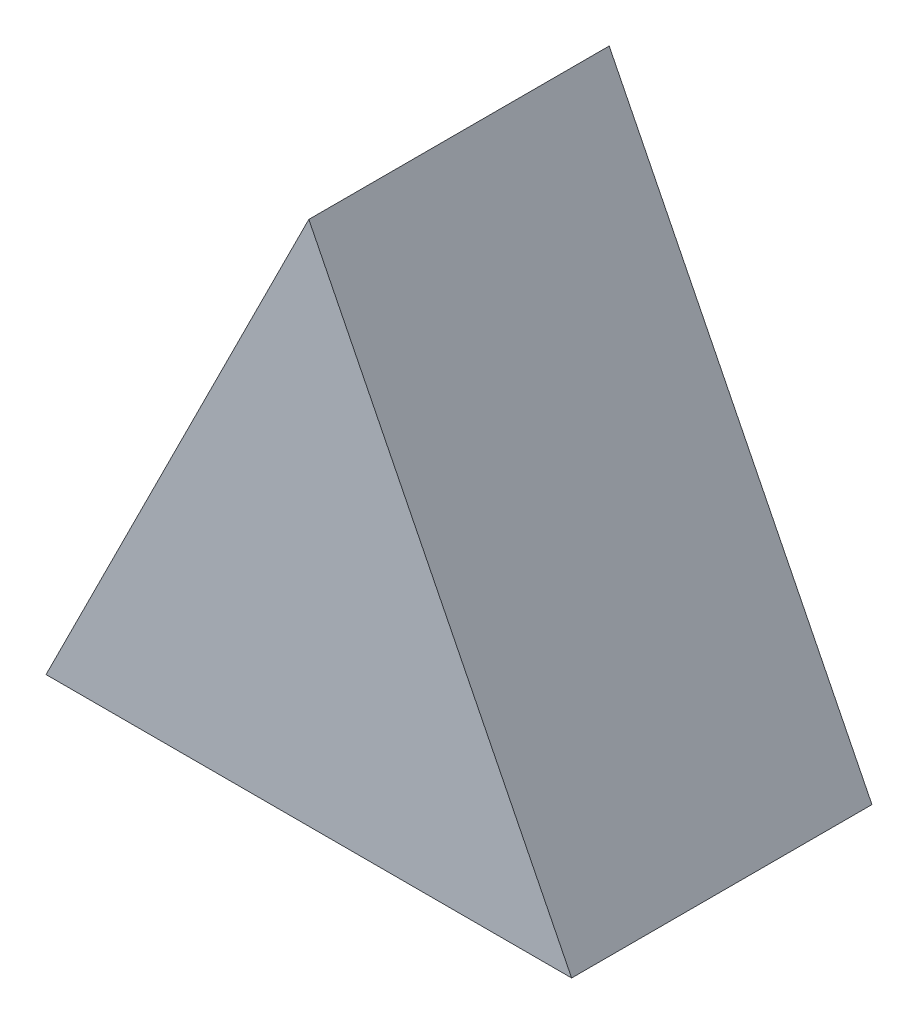
SolidWorks part; units mm, degrees
ref_plane "Front Plane" through (0, 0, 0) normal (0, 0, 1) x (1, 0, 0)
ref_plane "Top Plane" through (0, 0, 0) normal (0, 1, 0) x (1, 0, 0)
ref_plane "Right Plane" through (0, 0, 0) normal (1, 0, 0) x (0, 0, -1)
sketch "Sketch1" plane through (0, 0, 0) normal (0, 0, 1) x (1, 0, 0)
  line L0 (-5.7659, 17.7023) -> (11.7341, -17.2977)
  line L1 (11.7341, -17.2977) -> (-23.2659, -17.2977)
  line L2 (-23.2659, -17.2977) -> (-5.7659, 17.7023)
  point P3 (-5.7659, -17.2977)
  dimension "D1" = 35
  dimension "D2" = 35
extrude "Boss-Extrude1" add sketch "Sketch1" along normal blind 20
